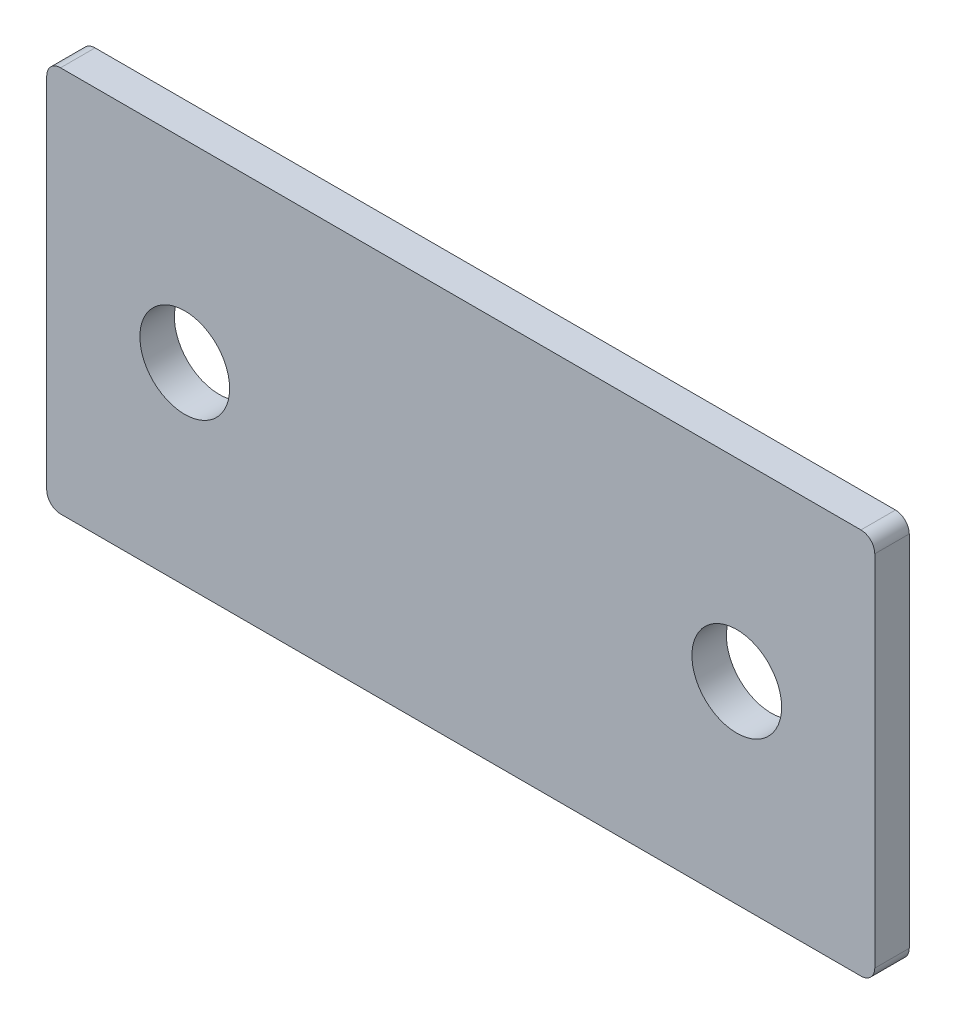
SolidWorks part; units mm, degrees
ref_plane "Спереди" through (0, 0, 0) normal (0, 0, 1) x (1, 0, 0)
ref_plane "Сверху" through (0, 0, 0) normal (0, 1, 0) x (1, 0, 0)
ref_plane "Справа" through (0, 0, 0) normal (1, 0, 0) x (0, 0, -1)
sketch "Эскиз1" plane through (0, 0, 0) normal (0, 0, 1) x (1, 0, 0)
  line L5 (-20, 0) -> (20, 0) construction
  line L6 (-30, -14) -> (30, -14)
  line L11 (-30, -14) -> (-30, 14)
  line L12 (-30, 14) -> (30, 14)
  line L16 (30, -14) -> (30, 14)
  line L17 (-30, -14) -> (30, 14) construction
  line L18 (-30, 14) -> (30, -14) construction
  circle A6 centre (-20, 0) radius 3.25
  circle A7 centre (20, 0) radius 3.25
  point P0 (0, 0)
  dimension "D4" = 6.5
  dimension "D3" = 10
  dimension "D1" = 60
  dimension "D2" = 28
extrude "Бобышка-Вытянуть1" add sketch "Эскиз1" along normal blind 2.5
fillet "Скругление1" radius 1 4 edges at (-30, -14, 1.25) (-30, 14, 1.25) (30, -14, 1.25) (30, 14, 1.25)
